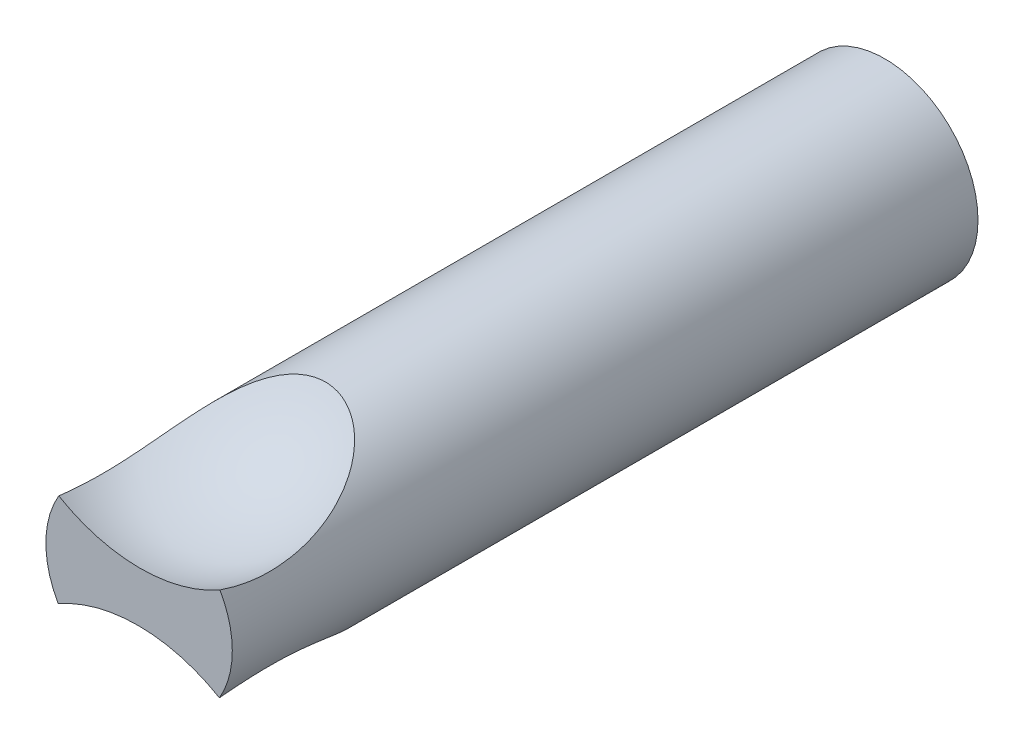
SolidWorks part; units mm, degrees
ref_plane "Front Plane" through (0, 0, 0) normal (0, 0, 1) x (1, 0, 0)
ref_plane "Top Plane" through (0, 0, 0) normal (0, 1, 0) x (1, 0, 0)
ref_plane "Right Plane" through (0, 0, 0) normal (1, 0, 0) x (0, 0, -1)
sketch "Sketch1" plane through (0, 0, 0) normal (0, 1, 0) x (1, 0, 0)
  line L0 (0, 0) -> (0, 101.6) construction
  line L1 (0, 101.6) -> (12.7, 101.6)
  line L2 (12.7, 101.6) -> (12.7, 0)
  line L3 (12.7, 0) -> (0, 0)
  line L4 (0, 0) -> (0, 101.6)
  dimension "D1" = 12.7
  dimension "D2" = 101.6
revolve "Revolve1" add sketch "Sketch1" angle 360 about L0
ref_plane "Plane1" through (0, 25.4, 0) normal (0, -1, 0) x (-1, 0, 0)
sketch "Sketch5" plane through (0, 25.4, 0) normal (0, -1, 0) x (-1, 0, 0)
  line L0 (22.7185, 6.35) -> (-23.0015, 6.35) construction
  line L1 (22.7185, 6.35) -> (-23.0015, 6.35)
  arc A0 (22.7185, 6.35) -> (-23.0015, 6.35) centre (-0.1415, 6.35) cw
  point P6 (32.09, -7.93)
revolve "Cut-Revolve1" cut sketch "Sketch5" angle 360 about L0
ref_plane "Plane2" through (0, -25.4, 0) normal (0, 1, 0) x (1, 0, 0)
sketch "Sketch6" plane through (0, -25.4, 0) normal (0, 1, 0) x (1, 0, 0)
  line L1 (22.7185, 6.35) -> (-23.0015, 6.35)
  arc A0 (22.7185, 6.35) -> (-23.0015, 6.35) centre (-0.1415, 6.35) cw
  point P6 (32.09, -7.93)
revolve "Cut-Revolve2" cut sketch "Sketch6" angle 360 about L1
